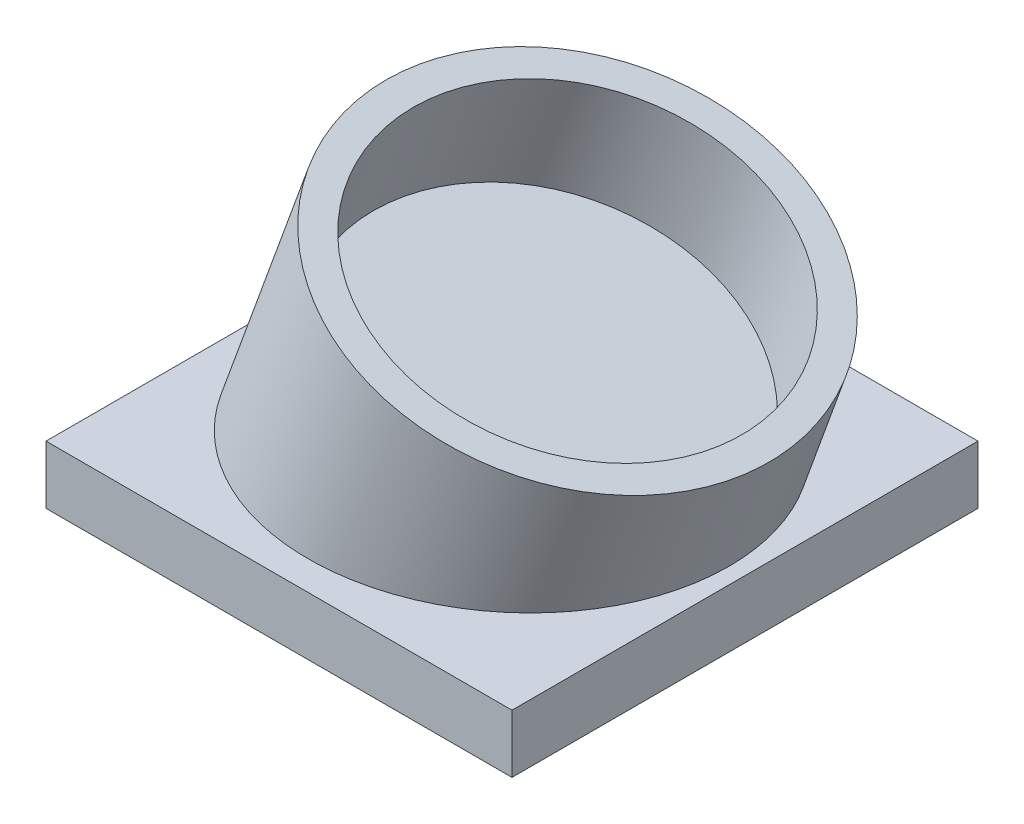
SolidWorks part; units mm, degrees
ref_plane "Front Plane" through (0, 0, 0) normal (0, 0, 1) x (1, 0, 0)
ref_plane "Top Plane" through (0, 0, 0) normal (0, 1, 0) x (1, 0, 0)
ref_plane "Right Plane" through (0, 0, 0) normal (1, 0, 0) x (0, 0, -1)
sketch "Sketch1" plane through (0, 0, 0) normal (0, 1, 0) x (1, 0, 0)
  line L1 (0, 0) -> (101.6, 0)
  line L2 (0, 0) -> (0, 101.6)
  line L3 (0, 101.6) -> (101.6, 101.6)
  line L4 (101.6, 0) -> (101.6, 101.6)
  dimension "D1" = 101.6
  dimension "D2" = 101.6
extrude "Boss-Extrude1" add sketch "Sketch1" along normal blind 12.7
ref_plane "Plane2" through (15.9666, 43.868, 0) normal (0.342, 0.9397, 0) x (0, 0, -1)
sketch "Sketch4" plane through (15.9666, 43.868, 0) normal (0.342, 0.9397, 0) x (0, 0, -1)
  line L0 (101.6, 4.3437) -> (0, 4.3437) construction
  line L1 (0, 4.3437) -> (0, -91.1291) construction
  circle A0 centre (50.8, -43.3927) radius 38.1
  circle A1 centre (50.8, -43.3927) radius 44.45
  point P4 (50.8, 4.3437)
  point P7 (0, -43.3927)
  dimension "D1" = 76.2
  dimension "D2" = 6.35
extrude "Boss-Extrude5" add sketch "Sketch4" against normal blind 1 separate body
sketch "Sketch7" plane through (15.6246, 42.9283, 0) normal (-0.342, -0.9397, 0) x (0.9397, -0.342, 0)
  circle A0 centre (43.3927, -50.8) radius 44.45
  dimension "D1" = 88.9
extrude "Boss-Extrude6" add sketch "Sketch7" along normal up to surface (0.1961 mm away)
sketch "Sketch8" plane through (15.9666, 43.868, 0) normal (0.342, 0.9397, 0) x (0.9397, -0.342, 0)
  circle A0 centre (43.3927, 50.8) radius 38.1
  circle A1 centre (43.3927, 50.8) radius 44.45
  dimension "D1" = 76.2
  dimension "D2" = 6.35
extrude "Boss-Extrude7" add sketch "Sketch8" along normal blind 24.4
